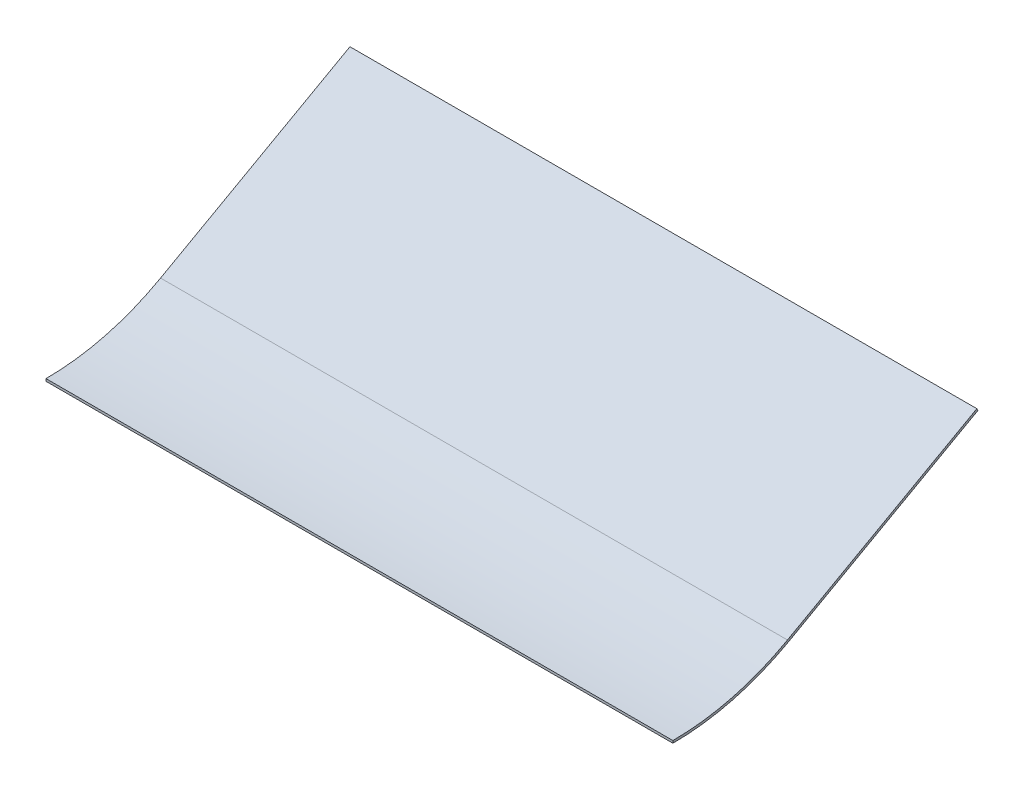
SolidWorks part; units mm, degrees
ref_plane "Front Plane" through (0, 0, 0) normal (0, 0, 1) x (1, 0, 0)
ref_plane "Top Plane" through (0, 0, 0) normal (0, 1, 0) x (1, 0, 0)
ref_plane "Right Plane" through (0, 0, 0) normal (1, 0, 0) x (0, 0, -1)
sketch "Sketch1" plane through (0, 0, 0) normal (1, 0, 0) x (0, 0, -1)
  line L0 (0, 0) -> (203.2, 0) construction
  line L1 (203.2, -66.6876) -> (76.5904, -137.3096)
  line L2 (0, 0) -> (0, -157.226) construction
  line L3 (203.2, 0) -> (203.2, -66.6876) construction
  arc A0 (0, -157.226) -> (76.5904, -137.3096) centre (0, 0) ccw
  dimension "D1" = 314.452
  dimension "D2" = 203.2
  dimension "D3" = 29.152
extrude "Extrude-Thin1" add sketch "Sketch1" along normal blind 419.1 thin thin type one direction wall 1.5875
